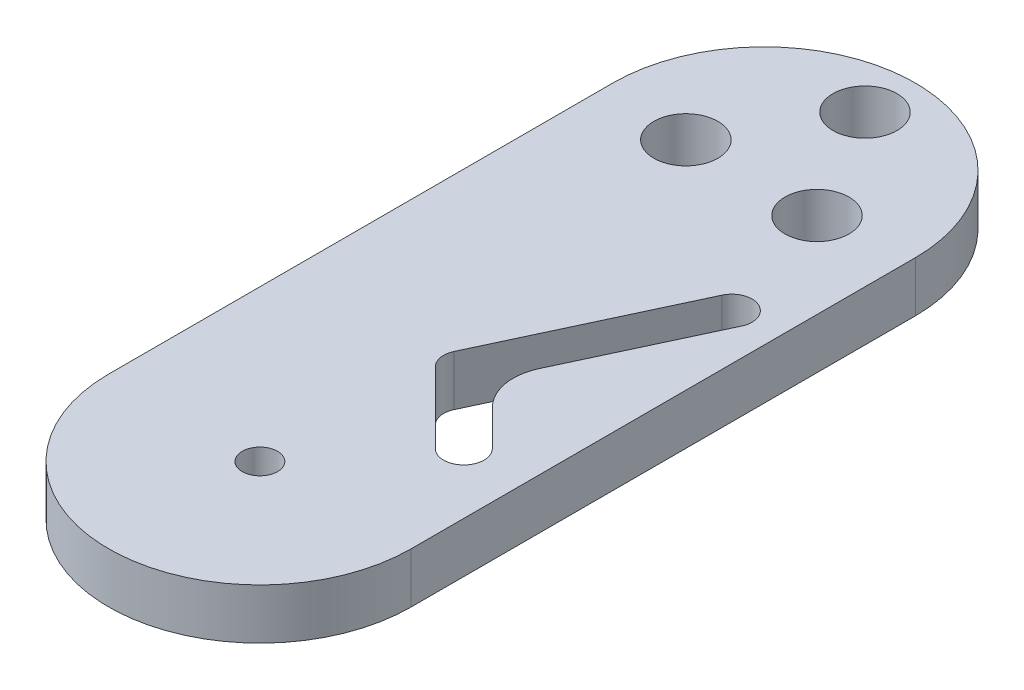
SolidWorks part; units mm, degrees
ref_plane "Front Plane" through (0, 0, 0) normal (0, 0, 1) x (1, 0, 0)
ref_plane "Top Plane" through (0, 0, 0) normal (0, 1, 0) x (1, 0, 0)
ref_plane "Right Plane" through (0, 0, 0) normal (1, 0, 0) x (0, 0, -1)
sketch "Sketch1" plane through (0, 0, 0) normal (0, 1, 0) x (1, 0, 0)
  line L0 (0, 0) -> (0, 50) construction
  line L1 (-15, 0) -> (-15, 50)
  line L2 (15, 0) -> (15, 50)
  line L3 (10.4451, 36.3547) -> (1.9927, 18.2286) construction
  line L4 (12.2577, 35.5095) -> (4.3972, 18.6526)
  line L5 (8.6325, 37.2) -> (0.1801, 19.0738)
  line L6 (0, 65) -> (0, 60) construction
  line L7 (0, 60) -> (-6.5, 48.7417) construction
  line L8 (-6.5, 48.7417) -> (6.5, 48.7417) construction
  line L9 (6.5, 48.7417) -> (0, 60) construction
  line L10 (3.0809, 20.3492) -> (9, 11.2213) construction
  line L11 (4.3972, 18.6526) -> (10.4142, 12.6355)
  line L12 (0.5785, 16.8144) -> (7.5858, 9.8071)
  arc A0 (-15, 0) -> (15, 0) centre (0, 0) ccw
  arc A1 (15, 50) -> (-15, 50) centre (0, 50) ccw
  circle A2 centre (0, 0) radius 1.75
  arc A3 (12.2577, 35.5095) -> (8.6325, 37.2) centre (10.4451, 36.3547) ccw
  arc A4 (0.1801, 19.0738) -> (0.5785, 16.8144) centre (1.9927, 18.2286) ccw
  circle A5 centre (0, 60) radius 3.175
  circle A6 centre (-6.5, 48.7417) radius 3.175
  circle A7 centre (6.5, 48.7417) radius 3.175
  arc A9 (0.1801, 19.0738) -> (0.5785, 16.8144) centre (1.9927, 18.2286) ccw
  arc A10 (7.5858, 9.8071) -> (10.4142, 12.6355) centre (9, 11.2213) ccw
  point P3 (0, 25)
  point P12 (6.2189, 27.2917)
  point P24 (5.4964, 12.8256)
  dimension "D1" = 15
  dimension "D2" = 3.5
  dimension "D4" = 2
  dimension "D7" = 6.35
  dimension "D8" = 5
  dimension "D12" = 110
  dimension "D3" = 50
  dimension "D5" = 25
  dimension "D6" = 20
  dimension "D9" = 13
  dimension "D10" = 13
  dimension "D11" = 6
extrude "Boss-Extrude1" add sketch "Sketch1" along normal blind 5 contours L2 A1 L1 A0 A10 L12 A4 L5 A3 L4 L11 A7 A6 A5 A2
fillet "Fillet1" radius 5 1 edges at (4.3972, 2.5, -18.6526)
